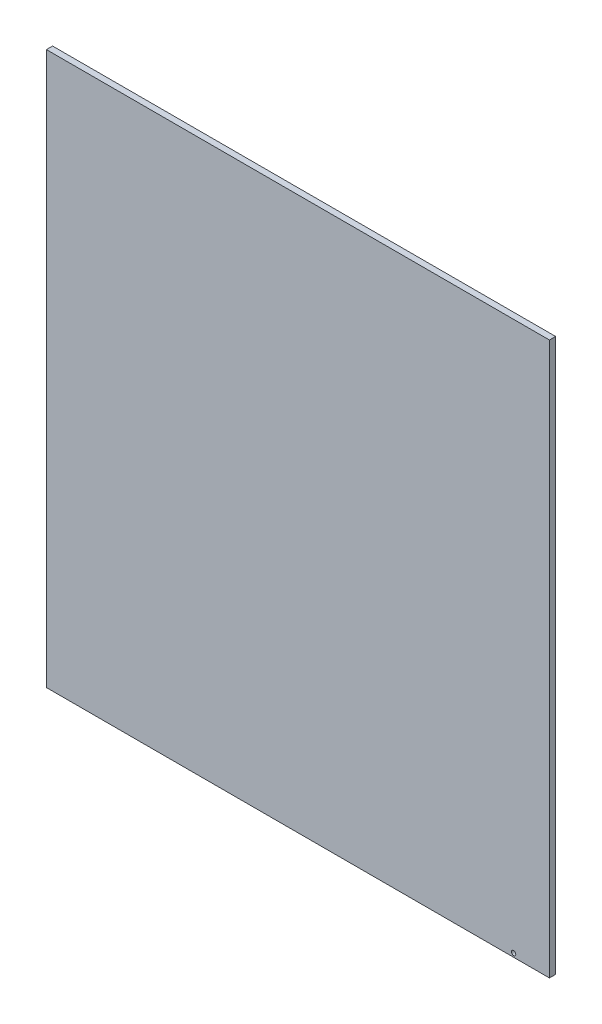
SolidWorks part; units mm, degrees
ref_plane "Front Plane" through (0, 0, 0) normal (0, 0, 1) x (1, 0, 0)
ref_plane "Top Plane" through (0, 0, 0) normal (0, 1, 0) x (1, 0, 0)
ref_plane "Right Plane" through (0, 0, 0) normal (1, 0, 0) x (0, 0, -1)
sketch "Sketch1" plane through (0, 0, 0) normal (0, 0, 1) x (1, 0, 0)
  line L1 (0, 0) -> (407, 0)
  line L2 (0, 0) -> (0, 450)
  line L3 (0, 450) -> (407, 450)
  line L4 (407, 0) -> (407, 450)
  dimension "D1" = 407
  dimension "D2" = 450
extrude "Boss-Extrude1" add sketch "Sketch1" along normal blind 5
sketch "Sketch4" plane through (0, 0, 0) normal (0, 0, -1) x (-1, 0, 0)
  line L0 (-407, 0) -> (-407, 450) construction
  line L1 (-407, 450) -> (0, 450) construction
  line L2 (0, 225) -> (-144.3104, 225) construction
  line L3 (0, 450) -> (0, 0) construction
  circle A0 centre (-378, 447) radius 1.75
  dimension "D1" = 3.5
  dimension "D2" = 29
  dimension "D3" = 3
extrude "Cut-Extrude3" cut sketch "Sketch4" against normal through all
sketch "Sketch5" plane through (0, 0, 0) normal (0, 0, -1) x (-1, 0, 0)
  line L0 (0, 0) -> (-407, 0) construction
  line L1 (-0.1194, 0) -> (-407, 0)
  line L2 (-0.1194, 0) -> (-0.1194, -4)
  line L3 (-0.1194, -4) -> (-407, -4)
  line L4 (-407, 0) -> (-407, -4)
  line L5 (-407, 0) -> (-407, 450) construction
  dimension "D1" = 4
extrude "Boss-Extrude2" add sketch "Sketch5" against normal blind 5
sketch "Sketch6" plane through (0, 0, 0) normal (0, 0, -1) x (-1, 0, 0)
  line L0 (-407, -4) -> (-407, 450) construction
  line L1 (-407, -4) -> (-0.1194, -4) construction
  circle A0 centre (-378, -1) radius 1.75
  dimension "D3" = 3.5
  dimension "D1" = 29
  dimension "D2" = 3
extrude "Cut-Extrude4" cut sketch "Sketch6" against normal through all
sketch "Sketch7" plane through (0, 0, 5) normal (0, 0, 1) x (1, 0, 0)
  line L0 (407, -4) -> (407, 450) construction
  line L1 (0, 450) -> (407, 450)
  line L2 (0, 450) -> (0, 443)
  line L3 (0, 443) -> (407, 443)
  line L4 (407, 450) -> (407, 443)
  dimension "D1" = 7
extrude "Cut-Extrude5" cut sketch "Sketch7" against normal blind 10
